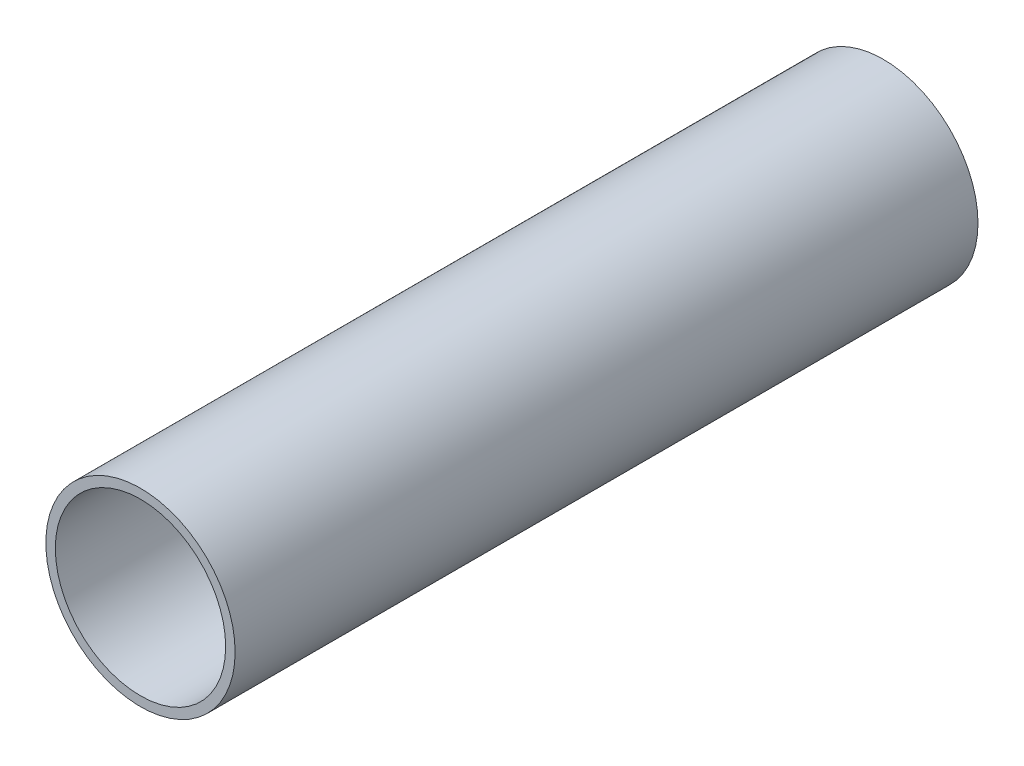
SolidWorks part; units mm, degrees
material "PET"
ref_plane "Front Plane" through (0, 0, 0) normal (0, 0, 1) x (1, 0, 0)
ref_plane "Top Plane" through (0, 0, 0) normal (0, 1, 0) x (1, 0, 0)
ref_plane "Right Plane" through (0, 0, 0) normal (1, 0, 0) x (0, 0, -1)
sketch "Sketch1" plane through (0, 0, 0) normal (0, 0, 1) x (1, 0, 0)
  circle A0 centre (0, 0) radius 20
  circle A1 centre (0, 0) radius 18
  dimension "D1" = 40
  dimension "D2" = 2
extrude "Boss-Extrude1" add sketch "Sketch1" along normal blind 157
